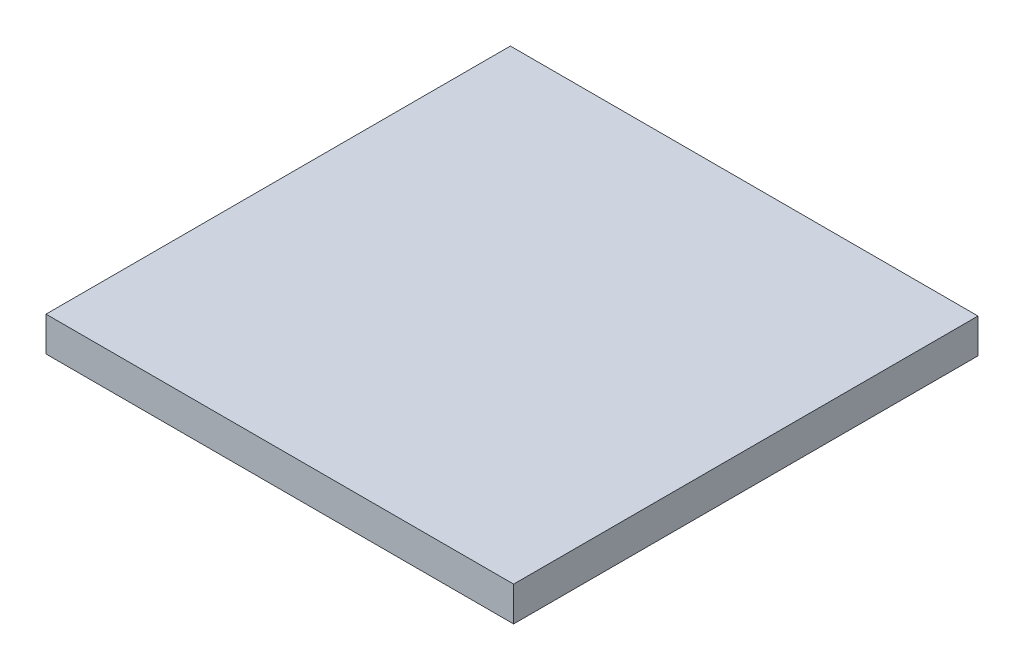
SolidWorks part; units mm, degrees
ref_plane "Front Plane" through (0, 0, 0) normal (0, 0, 1) x (1, 0, 0)
ref_plane "Top Plane" through (0, 0, 0) normal (0, 1, 0) x (1, 0, 0)
ref_plane "Right Plane" through (0, 0, 0) normal (1, 0, 0) x (0, 0, -1)
sketch "Sketch1" plane through (0, 0, 0) normal (0, 1, 0) x (1, 0, 0)
  line L1 (-56.2695, 31.3006) -> (-21.8627, 31.3006)
  line L2 (-56.2695, 31.3006) -> (-56.2695, -2.8672)
  line L3 (-56.2695, -2.8672) -> (-21.8627, -2.8672)
  line L4 (-21.8627, 31.3006) -> (-21.8627, -2.8672)
extrude "Boss-Extrude1" add sketch "Sketch1" along normal blind 2.54
